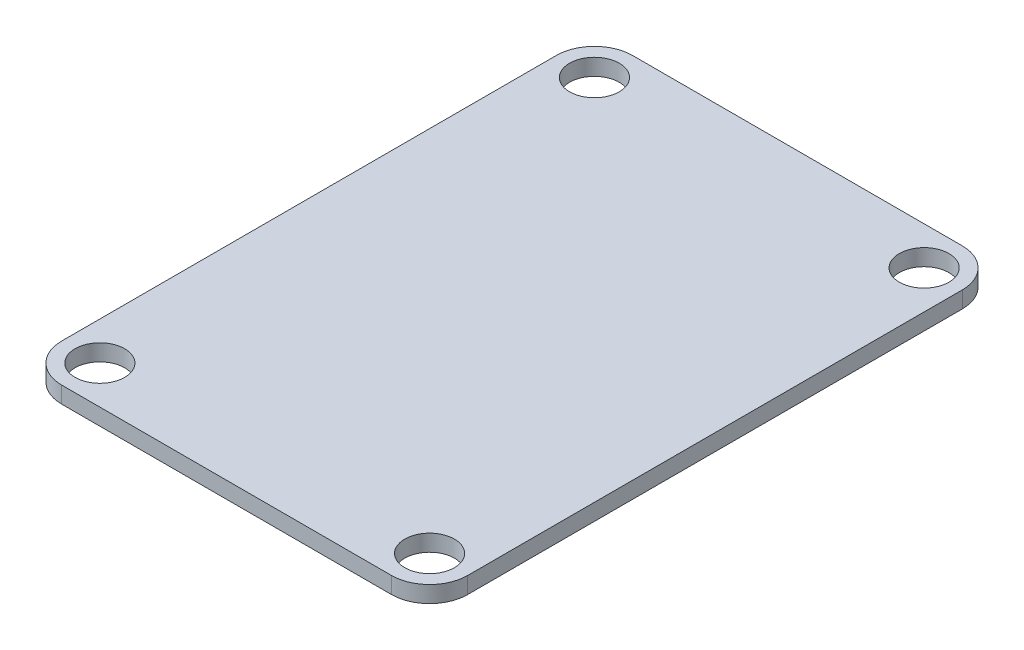
SolidWorks part; units mm, degrees
ref_plane "Front Plane" through (0, 0, 0) normal (0, 0, 1) x (1, 0, 0)
ref_plane "Top Plane" through (0, 0, 0) normal (0, 1, 0) x (1, 0, 0)
ref_plane "Right Plane" through (0, 0, 0) normal (1, 0, 0) x (0, 0, -1)
sketch "Sketch1" plane through (0, 0, 0) normal (0, 1, 0) x (1, 0, 0)
  line L0 (-15.94, 23.91) -> (15.94, 23.91) construction
  line L1 (15.94, 23.91) -> (15.94, -23.91) construction
  line L2 (15.94, -23.91) -> (-15.94, -23.91) construction
  line L3 (-15.94, -23.91) -> (-15.94, 23.91) construction
  line L7 (-15.94, 27.6) -> (15.94, 27.6)
  line L8 (-19.63, 23.91) -> (-19.63, -23.91)
  line L9 (-15.94, -27.6) -> (15.94, -27.6)
  line L10 (19.63, 23.91) -> (19.63, -23.91)
  line L11 (-19.63, 27.6) -> (19.63, -27.6) construction
  line L12 (-19.63, -27.6) -> (19.63, 27.6) construction
  arc A0 (-19.63, -23.91) -> (-15.94, -27.6) centre (-15.94, -23.91) ccw
  arc A1 (15.94, -27.6) -> (19.63, -23.91) centre (15.94, -23.91) ccw
  arc A2 (15.94, 27.6) -> (19.63, 23.91) centre (15.94, 23.91) cw
  arc A3 (-15.94, 27.6) -> (-19.63, 23.91) centre (-15.94, 23.91) ccw
  circle A4 centre (-15.94, 23.91) radius 2.4
  circle A5 centre (15.94, 23.91) radius 2.4
  circle A6 centre (15.94, -23.91) radius 2.4
  circle A7 centre (-15.94, -23.91) radius 2.4
  point P0 (0, 0)
  point P6 (0, 0)
  dimension "D3" = 3.69
  dimension "D4" = 39.26
  dimension "D1" = 4.8
  dimension "D2" = 31.88
  dimension "D5" = 55.2
extrude "Boss-Extrude1" add sketch "Sketch1" along normal blind 1.6
